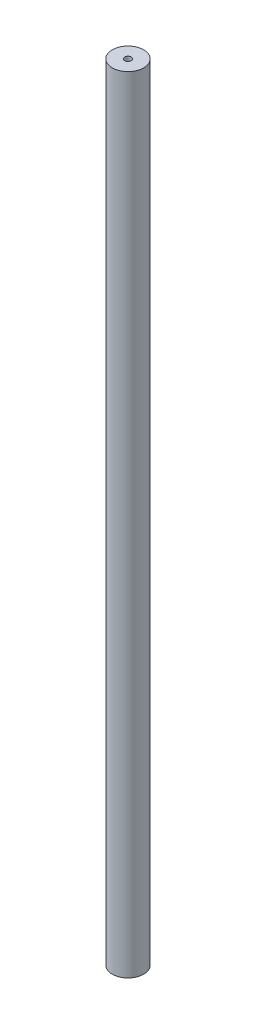
SolidWorks part; units mm, degrees
ref_plane "Front Plane" through (0, 0, 0) normal (0, 0, 1) x (1, 0, 0)
ref_plane "Top Plane" through (0, 0, 0) normal (0, 1, 0) x (1, 0, 0)
ref_plane "Right Plane" through (0, 0, 0) normal (1, 0, 0) x (0, 0, -1)
sketch "Sketch1" plane through (0, 0, 0) normal (0, 1, 0) x (1, 0, 0)
  circle A0 centre (0, 0) radius 5
  dimension "D1" = 10
extrude "Boss-Extrude1" add sketch "Sketch1" along normal blind 250
sketch "Sketch2" plane through (0, 0, 0) normal (0, -1, 0) x (-1, 0, 0)
  point P0 (0, 0)
hole_wizard "CSK for #1 Flat Head Socket Cap Screw1" positions "Sketch2" profile "Sketch3" countersink size "#1" standard "ANSI Inch" end condition through all
sketch "Sketch3" plane through (0, 0, 0) normal (1, 0, 0) x (0, 0, -1)
  line L0 (0, 0) -> (0, 250)
  line L1 (0, 250) -> (1.0287, 250)
  line L2 (1.0287, 250) -> (1.0287, 1.271)
  line L3 (1.0287, 1.271) -> (2.1336, 0)
  line L5 (2.1336, 0) -> (0, 0)
  line L6 (-1.0287, 1.271) -> (-2.1336, 0) construction
  line L11 (0, -6.35) -> (0, 107.95) construction
  dimension "Thru Hole Dia." = 2.0574
  dimension "Thru Hole Depth" = 250
  dimension "Near C'Sink Dia." = 4.2672
  dimension "Near C'Sink Angle" = 82
